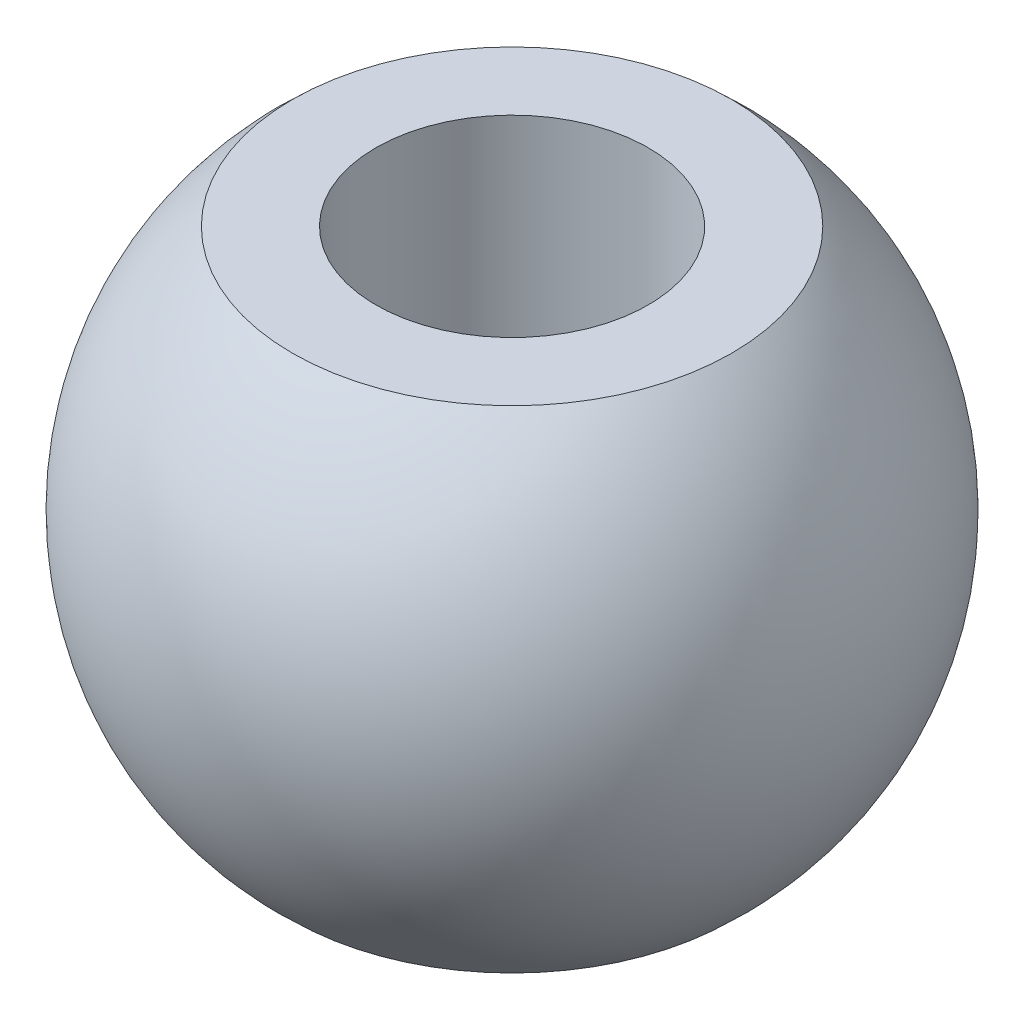
SolidWorks part; units mm, degrees
ref_plane "Front Plane" through (0, 0, 0) normal (0, 0, 1) x (1, 0, 0)
ref_plane "Top Plane" through (0, 0, 0) normal (0, 1, 0) x (1, 0, 0)
ref_plane "Right Plane" through (0, 0, 0) normal (1, 0, 0) x (0, 0, -1)
sketch "Sketch2" plane through (0, 0, 0) normal (0, 0, 1) x (1, 0, 0)
  line L0 (0, 5.5902) -> (0, -5.5902)
  line L1 (0, 5.5902) -> (-5, 5.5902)
  line L3 (-5, -5.5902) -> (0, -5.5902)
  arc A0 (-5, 5.5902) -> (-5, -5.5902) centre (0, 0) ccw
  point P6 (0, 0)
  dimension "D1" = 15
  dimension "D2" = 5
revolve "Revolve1" add sketch "Sketch2" angle 360 about L0
sketch "Sketch3" plane through (0, 5.5902, 0) normal (0, 1, 0) x (1, 0, 0)
  circle A0 centre (0, 0) radius 3.1
  dimension "D1" = 6.2
extrude "Cut-Extrude1" cut sketch "Sketch3" against normal through all
